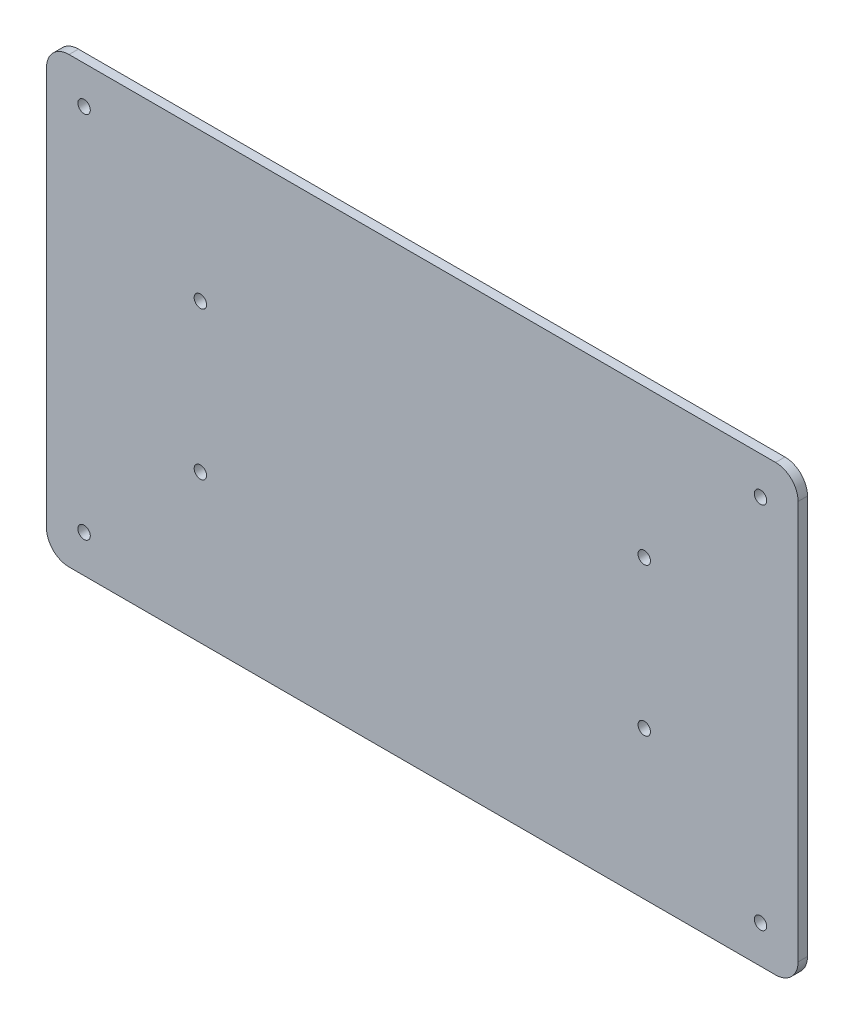
SolidWorks part; units mm, degrees
ref_plane "Front Plane" through (0, 0, 0) normal (0, 0, 1) x (1, 0, 0)
ref_plane "Top Plane" through (0, 0, 0) normal (0, 1, 0) x (1, 0, 0)
ref_plane "Right Plane" through (0, 0, 0) normal (1, 0, 0) x (0, 0, -1)
sketch "Sketch1" plane through (0, 0, 0) normal (0, 0, 1) x (1, 0, 0)
  line L0 (-127, -62.3) -> (127, -62.3) construction
  line L1 (-119.38, 75) -> (119.38, 75)
  line L2 (-127, 67.38) -> (-127, -67.38)
  line L3 (-119.38, -75) -> (119.38, -75)
  line L4 (127, 67.38) -> (127, -67.38)
  line L5 (-127, 75) -> (127, -75) construction
  line L6 (-127, -75) -> (127, 75) construction
  line L7 (-127, 62.3) -> (127, 62.3) construction
  line L8 (-75, 25) -> (75, 25) construction
  line L9 (-75, 25) -> (-75, -25) construction
  line L10 (-75, -25) -> (75, -25) construction
  line L11 (75, 25) -> (75, -25) construction
  line L12 (-75, 25) -> (75, -25) construction
  line L13 (-75, -25) -> (75, 25) construction
  circle A0 centre (-75, 25) radius 2.1
  circle A1 centre (-75, -25) radius 2.1
  circle A2 centre (75, -25) radius 2.1
  circle A3 centre (75, 25) radius 2.1
  circle A4 centre (-114.3, 62.3) radius 2.1
  circle A5 centre (114.3, 62.3) radius 2.1
  circle A6 centre (-114.3, -62.3) radius 2.1
  circle A7 centre (114.3, -62.3) radius 2.1
  arc A8 (-127, -67.38) -> (-119.38, -75) centre (-119.38, -67.38) ccw
  arc A9 (119.38, 75) -> (127, 67.38) centre (119.38, 67.38) cw
  arc A10 (119.38, -75) -> (127, -67.38) centre (119.38, -67.38) ccw
  arc A11 (-119.38, 75) -> (-127, 67.38) centre (-119.38, 67.38) ccw
  point P0 (0, 0)
  point P8 (0, 0)
  dimension "D6" = 4.2
  dimension "D7" = 4.2
  dimension "D8" = 4.2
  dimension "D9" = 4.2
  dimension "D15" = 4.2
  dimension "D16" = 4.2
  dimension "D17" = 4.2
  dimension "D18" = 4.2
  dimension "D19" = 7.62
  dimension "D1" = 254
  dimension "D2" = 150
  dimension "D3" = 12.7
  dimension "D4" = 50
  dimension "D5" = 150
  dimension "D10" = 12.7
  dimension "D11" = 12.7
  dimension "D12" = 12.7
  dimension "D13" = 12.7
  dimension "D14" = 12.7
extrude "Boss-Extrude1" add sketch "Sketch1" along normal blind 3.175 contours A2 | A3 | L1 A9 L4 A10 L3 A8 L2 A11 | A4 | A5 | A7 | A6 | A0 | A1
sketch "PS footprint" plane through (0, 0, 3.175) normal (0, 0, 1) x (1, 0, 0)
  line L1 (-107.95, 57.15) -> (107.95, 57.15)
  line L2 (-107.95, 57.15) -> (-107.95, -57.15)
  line L3 (-107.95, -57.15) -> (107.95, -57.15)
  line L4 (107.95, 57.15) -> (107.95, -57.15)
  line L5 (-107.95, 57.15) -> (107.95, -57.15) construction
  line L6 (-107.95, -57.15) -> (107.95, 57.15) construction
  point P0 (0, 0)
  dimension "D1" = 114.3
  dimension "D2" = 215.9
equation "\"Plate-Frame\" = 4.2mm"
